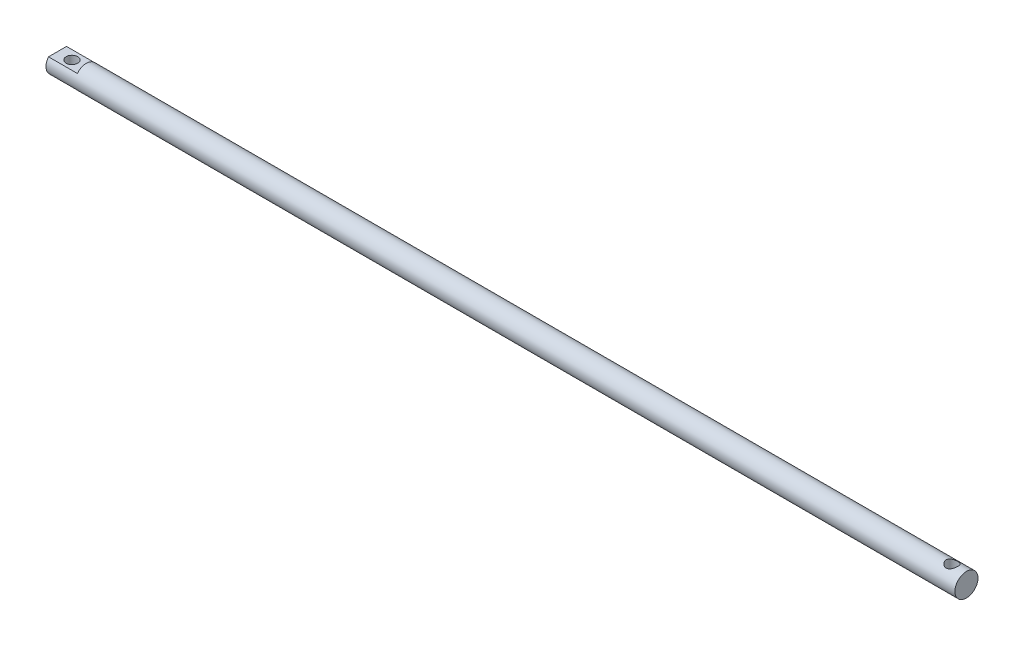
SolidWorks part; units mm, degrees
material "普通碳钢"
ref_plane "前视基准面" through (0, 0, 0) normal (0, 0, 1) x (1, 0, 0)
ref_plane "上视基准面" through (0, 0, 0) normal (0, 1, 0) x (1, 0, 0)
ref_plane "右视基准面" through (0, 0, 0) normal (1, 0, 0) x (0, 0, -1)
sketch "草图1" plane through (0, 0, 0) normal (1, 0, 0) x (0, 0, -1)
  circle A0 centre (0, 0) radius 8
  dimension "D1" = 16
extrude "凸台-拉伸1" add sketch "草图1" along normal blind 630
sketch "草图3" plane through (0, 0, 0) normal (-1, 0, 0) x (0, 0, 1)
  line L5 (-10, -5) -> (10, -5)
  line L6 (-10, -5) -> (-10, 5)
  line L7 (-10, 5) -> (10, 5)
  line L8 (10, -5) -> (10, 5)
  dimension "D1" = 10
  dimension "D2" = 5
  dimension "D3" = 20
  dimension "D4" = 10
sketch "草图2" plane through (0, 0, 0) normal (0, 1, 0) x (1, 0, 0)
  line L0 (0, 0) -> (630, 0) construction
  line L1 (630, -8) -> (630, 8) construction
  line L2 (0, 8) -> (0, -8) construction
  circle A0 centre (10, 0) radius 4
  circle A1 centre (620, 0) radius 4
  dimension "D1" = 10
  dimension "D2" = 8
  dimension "D3" = 8
  dimension "D4" = 10
extrude "切除-拉伸1" cut sketch "草图2" against normal through all and the other way through all
extrude "切除-拉伸2" cut sketch "草图3" against normal blind 20 flip side to cut
